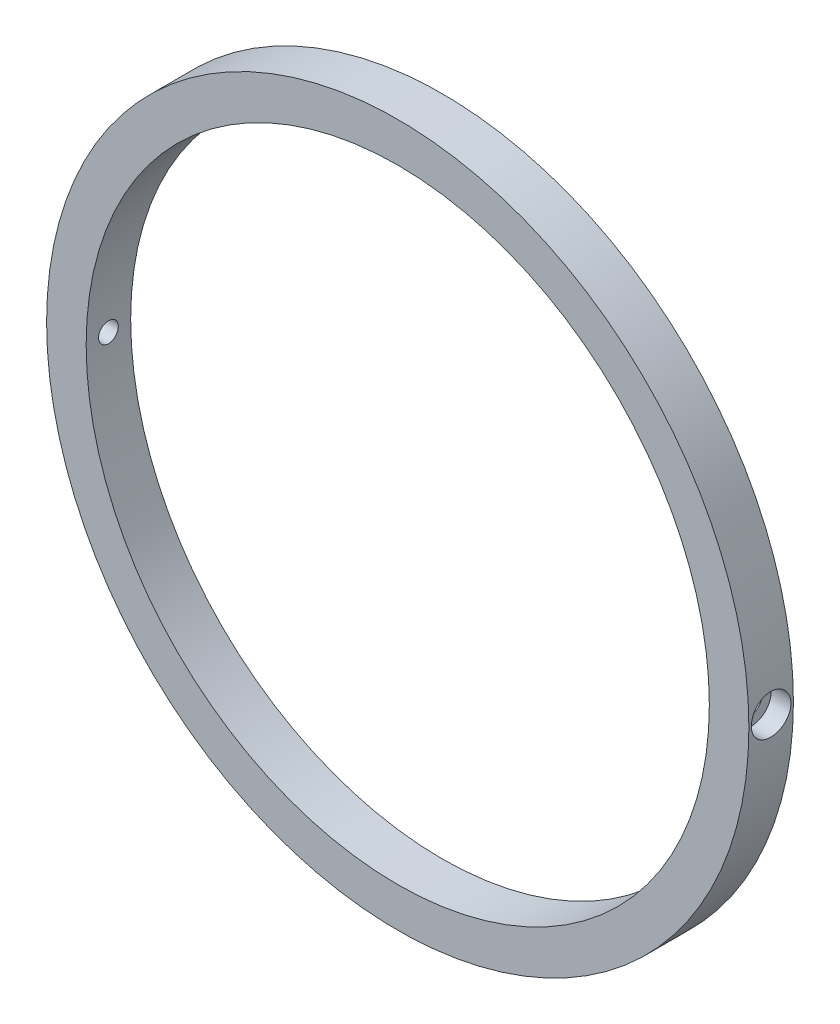
SolidWorks part; units mm, degrees
material "6061-T6 (SS)"
ref_plane "Front Plane" through (0, 0, 0) normal (0, 0, 1) x (1, 0, 0)
ref_plane "Top Plane" through (0, 0, 0) normal (0, 1, 0) x (1, 0, 0)
ref_plane "Right Plane" through (0, 0, 0) normal (1, 0, 0) x (0, 0, -1)
sketch "Sketch1" plane through (0, 0, 0) normal (0, 0, 1) x (1, 0, 0)
  circle A0 centre (0, 0) radius 56.3562
  circle A1 centre (0, 0) radius 50.0062
  dimension "D1" = 112.7125
  dimension "D2" = 6.35
extrude "Boss-Extrude1" add sketch "Sketch1" along normal mid plane 7.1437
hole_wizard "Hole1" positions "3DSketch1" profile "Sketch3" legacy
sketch3d "3DSketch1"
  point P0 (56.3562, 0, 0)
  point P3 (0, 0, 0)
sketch "Sketch3" plane through (56.3562, 0, 0) normal (0, 1, 0) x (0, 0, -1)
  line L0 (0, 0) -> (0, 12.7)
  line L1 (0, 12.7) -> (1.5875, 12.7)
  line L2 (1.5875, 12.7) -> (1.5875, 3.175)
  line L3 (1.5875, 3.175) -> (3.175, 3.175)
  line L4 (3.175, 3.175) -> (3.175, 0)
  line L5 (3.175, 0) -> (0, 0)
  line L6 (0, 110) -> (0, -10) construction
  dimension "Diameter" = 3.175
  dimension "Depth" = 12.7
  dimension "C-Bore Diameter" = 6.35
  dimension "C-Bore Depth" = 3.175
mirror "Mirror1" about plane through (0, 0, 0) normal (1, 0, 0) of "Hole1"
